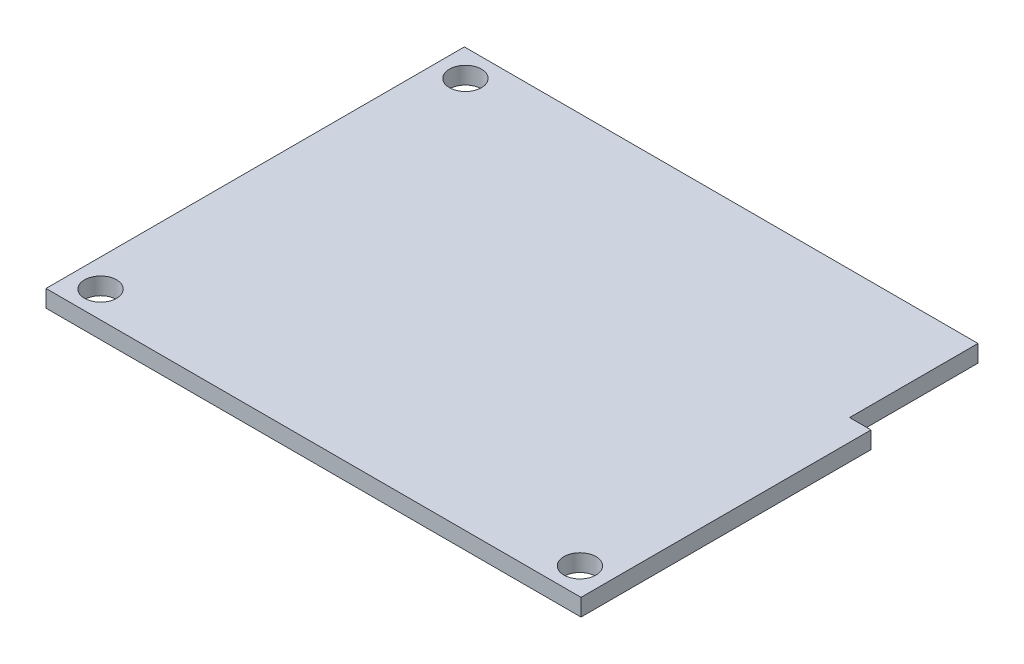
SolidWorks part; units mm, degrees
ref_plane "Front Plane" through (0, 0, 0) normal (0, 0, 1) x (1, 0, 0)
ref_plane "Top Plane" through (0, 0, 0) normal (0, 1, 0) x (1, 0, 0)
ref_plane "Right Plane" through (0, 0, 0) normal (1, 0, 0) x (0, 0, -1)
sketch "Sketch1" plane through (0, 0, 0) normal (0, 1, 0) x (1, 0, 0)
  line L0 (23, 19.55) -> (23, 7.55)
  line L1 (-25, -19.55) -> (25, -19.55)
  line L2 (-25, -19.55) -> (-25, 19.55)
  line L3 (-25, 19.55) -> (23, 19.55)
  line L4 (25, -19.55) -> (25, 7.55)
  line L5 (-25, -19.55) -> (25, 19.55) construction
  line L6 (-25, 19.55) -> (25, -19.55) construction
  line L7 (-22.4, -17.05) -> (22.4, -17.05) construction
  line L8 (-22.4, -17.05) -> (-22.4, 17.05) construction
  line L9 (-22.4, 17.05) -> (22.4, 17.05) construction
  line L10 (22.4, -17.05) -> (22.4, 17.05) construction
  line L11 (-22.4, -17.05) -> (22.4, 17.05) construction
  line L12 (-22.4, 17.05) -> (22.4, -17.05) construction
  line L13 (23, 7.55) -> (25, 7.55)
  line L14 (23, 19.55) -> (25, 19.55) construction
  line L15 (25, 19.55) -> (25, 7.55) construction
  circle A1 centre (-22.4, 17.05) radius 1.5
  circle A2 centre (-22.4, -17.05) radius 1.5
  circle A3 centre (22.4, -17.05) radius 1.5
  point P0 (0, 0)
  point P6 (0, 0)
  point P17 (23, 19.55)
  point P20 (25, 7.55)
  dimension "D5" = 3
  dimension "D6" = 3
  dimension "D7" = 3
  dimension "length" = 50
  dimension "width" = 39.1
  dimension "D3" = 44.8
  dimension "D1" = 34.1
  dimension "D2" = 2
  dimension "D4" = 12
extrude "Boss-Extrude1" add sketch "Sketch1" along normal blind 1.6
sketch "Sketch2" plane through (0, 1.6, 0) normal (0, 1, 0) x (1, 0, 0)
  circle A0 centre (-22.4, 17.05) radius 1.5
  circle A1 centre (-22.4, -17.05) radius 1.5
  circle A2 centre (22.4, -17.05) radius 1.5
  circle A3 centre (-22.4, 17.05) radius 2.5
  circle A4 centre (-22.4, -17.05) radius 2.5
  circle A5 centre (22.4, -17.05) radius 2.5
  point P10 (-22.4, 17.05)
  point P12 (-25.0379, -13.9529)
  point P14 (19.7539, -13.9529)
  point P16 (-22.4, -17.05)
  point P18 (22.4, -17.05)
  dimension "D1" = 3
  dimension "D2" = 5
equation "\"length\"=0.05"
equation "\"width\"=0.0391"
equation "\"D1@Sketch1\"=\"width\"-0.005"
